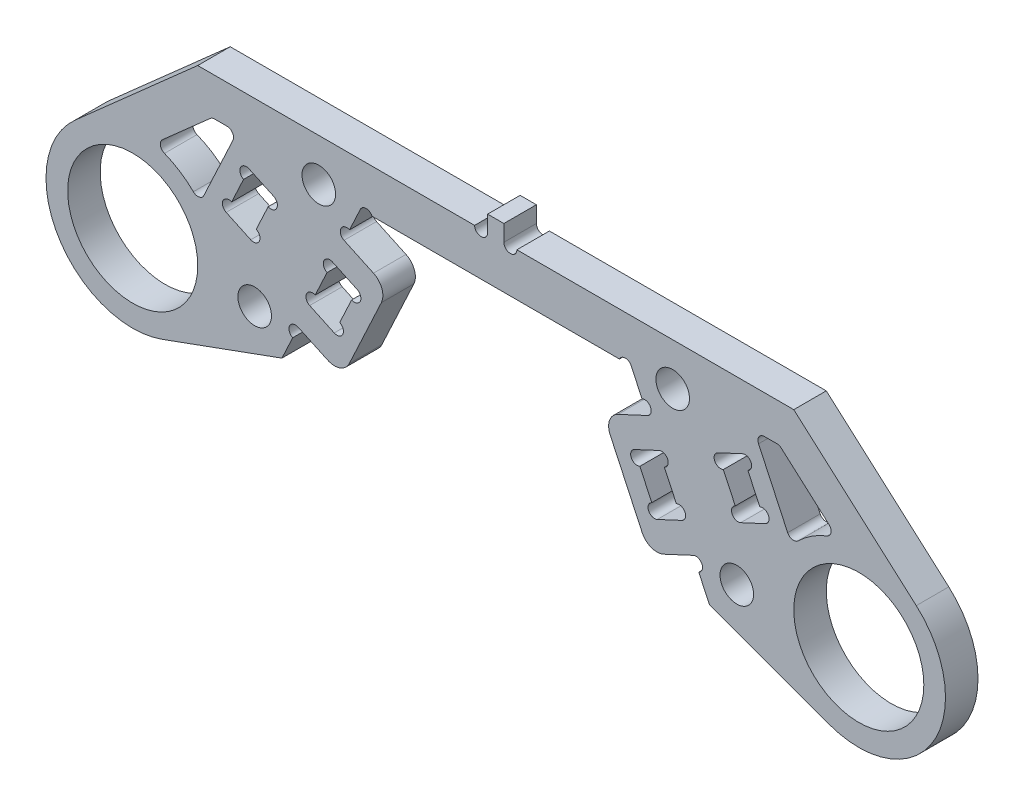
SolidWorks part; units mm, degrees
ref_plane "前视基准面" through (0, 0, 0) normal (0, 0, 1) x (1, 0, 0)
ref_plane "上视基准面" through (0, 0, 0) normal (0, 1, 0) x (1, 0, 0)
ref_plane "右视基准面" through (0, 0, 0) normal (1, 0, 0) x (0, 0, -1)
sketch "草图1" plane through (0, 0, 0) normal (0, 0, 1) x (1, 0, 0)
  line L0 (33.5, 0) -> (-33.5, 0) construction
  line L1 (-12.5, 12) -> (12.5, 12)
  line L2 (-12.5, 12) -> (-19.7282, -3.5009)
  line L3 (12.5, 12) -> (19.7282, -3.5009)
  line L4 (0, 12) -> (0, 0) construction
  line L5 (-30.7638, -7.5175) -> (-19.7282, -3.5009)
  line L6 (19.7282, -3.5009) -> (30.7638, -7.5175)
  line L7 (-38.804, 5.989) -> (-27.5, 16)
  line L8 (-27.5, 16) -> (27.5, 16)
  line L9 (27.5, 16) -> (38.804, 5.989)
  circle A0 centre (-33.5, 0) radius 6
  circle A1 centre (33.5, 0) radius 6
  arc A2 (-38.804, 5.989) -> (-30.7638, -7.5175) centre (-33.5, 0) ccw
  arc A3 (30.7638, -7.5175) -> (38.804, 5.989) centre (33.5, 0) ccw
  point P4 (0, 0)
  point P11 (0, 12)
  point P32 (0, 16)
  dimension "D1" = 67
  dimension "D2" = 12
  dimension "D3" = 2
  dimension "D4" = 25
  dimension "D5" = 12
  dimension "D6" = 50
  dimension "D7" = 4
  dimension "D8" = 140
  dimension "D9" = 55
extrude "凸台-拉伸1" add sketch "草图1" along normal mid plane 3
sketch "草图5" plane through (0, 0, 1.5) normal (0, 0, 1) x (1, 0, 0)
  line L0 (-14.001, 8.7811) -> (-9.9226, 6.8793)
  line L1 (-19.7282, -3.5009) -> (-12.5, 12) construction
  line L2 (-9.9226, 6.8793) -> (-14.1488, -2.1838)
  line L3 (-14.1488, -2.1838) -> (-18.2272, -0.282)
  line L4 (-18.2272, -0.282) -> (-14.001, 8.7811) construction
  line L5 (-14.001, 8.7811) -> (-15.0575, 6.5153)
  line L6 (-15.0575, 6.5153) -> (-12.7918, 5.4588)
  line L7 (-12.7918, 5.4588) -> (-14.9049, 0.9272)
  line L8 (-14.9049, 0.9272) -> (-17.1706, 1.9838)
  line L9 (-17.1706, 1.9838) -> (-18.2272, -0.282)
  line L10 (0, 12) -> (0, 0) construction
  line L11 (-12.5, 12) -> (12.5, 12) construction
  line L12 (14.9049, 0.9272) -> (17.1706, 1.9838)
  line L13 (12.7918, 5.4588) -> (14.9049, 0.9272)
  line L14 (15.0575, 6.5153) -> (12.7918, 5.4588)
  line L15 (14.001, 8.7811) -> (15.0575, 6.5153)
  line L16 (14.001, 8.7811) -> (9.9226, 6.8793)
  line L17 (9.9226, 6.8793) -> (14.1488, -2.1838)
  line L18 (14.1488, -2.1838) -> (18.2272, -0.282)
  line L19 (17.1706, 1.9838) -> (18.2272, -0.282)
  point P9 (-16.1141, 4.2496)
  dimension "D1" = 10
  dimension "D2" = 5
  dimension "D3" = 2.5
  dimension "D4" = 4.5
extrude "凸台-拉伸2" add sketch "草图5" against normal blind 3
sketch "草图6" plane through (0, 0, 1.5) normal (0, 0, 1) x (1, 0, 0)
  line L0 (-17.1706, 1.9838) -> (-15.0575, 6.5153) construction
  line L1 (-12.7918, 5.4588) -> (-14.9049, 0.9272) construction
  line L2 (-14.001, 8.7811) -> (-12.5, 12) construction
  line L3 (-19.7282, -3.5009) -> (-18.2272, -0.282) construction
  line L4 (0, 12) -> (0, 0) construction
  line L5 (-12.5, 12) -> (12.5, 12) construction
  line L6 (12.5, 12) -> (14.001, 8.7811) construction
  circle A0 centre (-15.3111, 5.9715) radius 0.6
  circle A1 centre (-13.0453, 4.915) radius 0.6
  circle A2 centre (-16.9171, 2.5276) radius 0.6
  circle A3 centre (-14.6513, 1.471) radius 0.6
  circle A4 centre (-13.7474, 9.3249) radius 0.6
  circle A5 centre (-18.4808, -0.8258) radius 0.6
  circle A6 centre (18.4808, -0.8258) radius 0.6
  circle A7 centre (13.7474, 9.3249) radius 0.6
  circle A8 centre (14.6513, 1.471) radius 0.6
  circle A9 centre (16.9171, 2.5276) radius 0.6
  circle A10 centre (13.0453, 4.915) radius 0.6
  circle A11 centre (15.3111, 5.9715) radius 0.6
  circle A12 centre (-11.9562, 11.7464) radius 0.6
  circle A13 centre (11.9562, 11.7464) radius 0.6
  dimension "D1" = 1.2
extrude "切除-拉伸2" cut sketch "草图6" against normal through all
fillet "圆角1" radius 1.5 4 edges at (9.9226, 6.8793, 0) (14.1488, -2.1838, 0) (-9.9226, 6.8793, 0) (-14.1488, -2.1838, 0)
sketch "草图7" plane through (0, 0, 1.5) normal (0, 0, 1) x (1, 0, 0)
  line L0 (-22.2445, -0.6154) -> (-16.3278, 12.0729) construction
  line L1 (-13.4939, 9.8687) -> (-12.5, 12) construction
  line L2 (-19.2862, 5.7287) -> (-13.8483, 3.193) construction
  line L3 (-13.2989, 4.3712) -> (-14.3977, 2.0148) construction
  line L4 (-19.7282, -3.5009) -> (-18.7343, -1.3696) construction
  line L5 (0, 12) -> (0, 0) construction
  line L6 (-11.4124, 12) -> (11.4124, 12) construction
  circle A0 centre (-22.2445, -0.6154) radius 1.55
  circle A1 centre (-16.3278, 12.0729) radius 1.55
  circle A2 centre (22.2445, -0.6154) radius 1.55
  circle A3 centre (16.3278, 12.0729) radius 1.55
  dimension "D1" = 3.1
  dimension "D2" = 14
  dimension "D3" = 3.5
extrude "切除-拉伸3" cut sketch "草图7" against normal through all
sketch "草图8" plane through (0, 0, 1.5) normal (0, 0, 1) x (1, 0, 0)
  line L0 (-26.173, 12.5) -> (-31.5318, 7.7541)
  line L1 (-21.1713, 0.5029) -> (-16.4947, 10.5319) construction
  line L2 (-27.5, 16) -> (-38.804, 5.989) construction
  line L8 (-14.9049, 0.9272) -> (-17.1706, 1.9838) construction
  line L9 (-16.6635, 3.0714) -> (-15.5647, 5.4278) construction
  line L10 (-26.173, 12.5) -> (-23.8523, 12.5)
  line L11 (27.5, 16) -> (-27.5, 16) construction
  line L12 (-16.1141, 4.2496) -> (-18.833, 5.5174) construction
  line L13 (0, 16) -> (0, 12) construction
  line L14 (-11.4124, 12) -> (11.4124, 12) construction
  line L27 (-13.2989, 4.3712) -> (-14.3977, 2.0148) construction
  line L28 (-15.0575, 6.5153) -> (-12.7918, 5.4588) construction
  line L29 (-14.9049, 0.9272) -> (-17.1706, 1.9838) construction
  line L30 (-13.2989, 4.3712) -> (-14.3977, 2.0148) construction
  line L31 (-15.0575, 6.5153) -> (-12.7918, 5.4588) construction
  line L32 (-16.6635, 3.0714) -> (-15.5647, 5.4278) construction
  line L33 (-22.1013, 5.6071) -> (-21.0025, 7.9635)
  line L34 (-20.4954, 9.051) -> (-22.7612, 10.1076)
  line L35 (-23.2683, 9.02) -> (-24.3671, 6.6636)
  line L36 (-24.8743, 5.576) -> (-22.6085, 4.5195)
  line L38 (24.8743, 5.576) -> (22.6085, 4.5195)
  line L40 (-27.3151, 5.0741) -> (-23.8523, 12.5)
  line L41 (23.2683, 9.02) -> (24.3671, 6.6636)
  line L42 (20.4954, 9.051) -> (22.7612, 10.1076)
  line L43 (22.1013, 5.6071) -> (21.0025, 7.9635)
  line L44 (26.173, 12.5) -> (23.8523, 12.5)
  line L45 (27.3151, 5.0741) -> (23.8523, 12.5)
  line L46 (26.173, 12.5) -> (31.5318, 7.7541)
  circle A1 centre (-33.5, 0) radius 6 construction
  arc A2 (-16.6635, 3.0714) -> (-17.1706, 1.9838) centre (-16.9171, 2.5276) ccw construction
  arc A4 (22.1013, 5.6071) -> (22.6085, 4.5195) centre (22.3549, 5.0633) ccw
  arc A6 (-14.9049, 0.9272) -> (-14.3977, 2.0148) centre (-14.6513, 1.471) ccw construction
  arc A7 (-13.2989, 4.3712) -> (-12.7918, 5.4588) centre (-13.0453, 4.915) ccw construction
  arc A8 (-15.0575, 6.5153) -> (-15.5647, 5.4278) centre (-15.3111, 5.9715) ccw construction
  arc A9 (-16.6635, 3.0714) -> (-17.1706, 1.9838) centre (-16.9171, 2.5276) ccw construction
  arc A10 (-14.9049, 0.9272) -> (-14.3977, 2.0148) centre (-14.6513, 1.471) ccw construction
  arc A11 (-13.2989, 4.3712) -> (-12.7918, 5.4588) centre (-13.0453, 4.915) ccw construction
  arc A12 (-15.0575, 6.5153) -> (-15.5647, 5.4278) centre (-15.3111, 5.9715) ccw construction
  arc A13 (-20.4954, 9.051) -> (-21.0025, 7.9635) centre (-20.749, 8.5072) cw
  arc A14 (-23.2683, 9.02) -> (-22.7612, 10.1076) centre (-23.0147, 9.5638) cw
  arc A15 (-24.8743, 5.576) -> (-24.3671, 6.6636) centre (-24.6207, 6.1198) cw
  arc A16 (-22.1013, 5.6071) -> (-22.6085, 4.5195) centre (-22.3549, 5.0633) cw
  arc A17 (24.8743, 5.576) -> (24.3671, 6.6636) centre (24.6207, 6.1198) ccw
  arc A18 (-27.3151, 5.0741) -> (-31.5318, 7.7541) centre (-33.5, 0) ccw
  circle A19 centre (-16.3278, 12.0729) radius 1.55 construction
  arc A20 (23.2683, 9.02) -> (22.7612, 10.1076) centre (23.0147, 9.5638) ccw
  arc A21 (20.4954, 9.051) -> (21.0025, 7.9635) centre (20.749, 8.5072) ccw
  arc A22 (27.3151, 5.0741) -> (31.5318, 7.7541) centre (33.5, 0) cw
  dimension "D1" = 3.5
  dimension "D2" = 2
  dimension "D4" = 0.5
  dimension "D3" = 2
  dimension "D5" = 3.5
extrude "切除-拉伸4" cut sketch "草图8" against normal through all
fillet "圆角2" radius 0.6 8 edges at (27.3151, 5.0741, 0) (23.8523, 12.5, 0) (31.5318, 7.7541, 0) (26.173, 12.5, 0) (-27.3151, 5.0741, 0) (-26.173, 12.5, 0) (-23.8523, 12.5, 0) (-31.5318, 7.7541, 0)
sketch "草图9" plane through (0, 0, 1.5) normal (0, 0, 1) x (1, 0, 0)
  line L0 (27.5, 16) -> (-27.5, 16) construction
  line L1 (-0.75, 17.5) -> (0.75, 17.5)
  line L2 (-0.75, 17.5) -> (-0.75, 16)
  line L3 (-0.75, 16) -> (0.75, 16)
  line L4 (0.75, 17.5) -> (0.75, 16)
  point P6 (0, 16)
  dimension "D1" = 1.5
  dimension "D2" = 1.5
extrude "凸台-拉伸3" add sketch "草图9" against normal up to surface (3 mm away)
sketch "草图10" plane through (0, 0, 1.5) normal (0, 0, 1) x (1, 0, 0)
  line L0 (27.5, 16) -> (0.75, 16) construction
  line L1 (-0.75, 16) -> (-27.5, 16) construction
  circle A0 centre (1.35, 16) radius 0.6
  circle A1 centre (-1.35, 16) radius 0.6
  dimension "D1" = 1.2
extrude "切除-拉伸5" cut sketch "草图10" against normal through all
